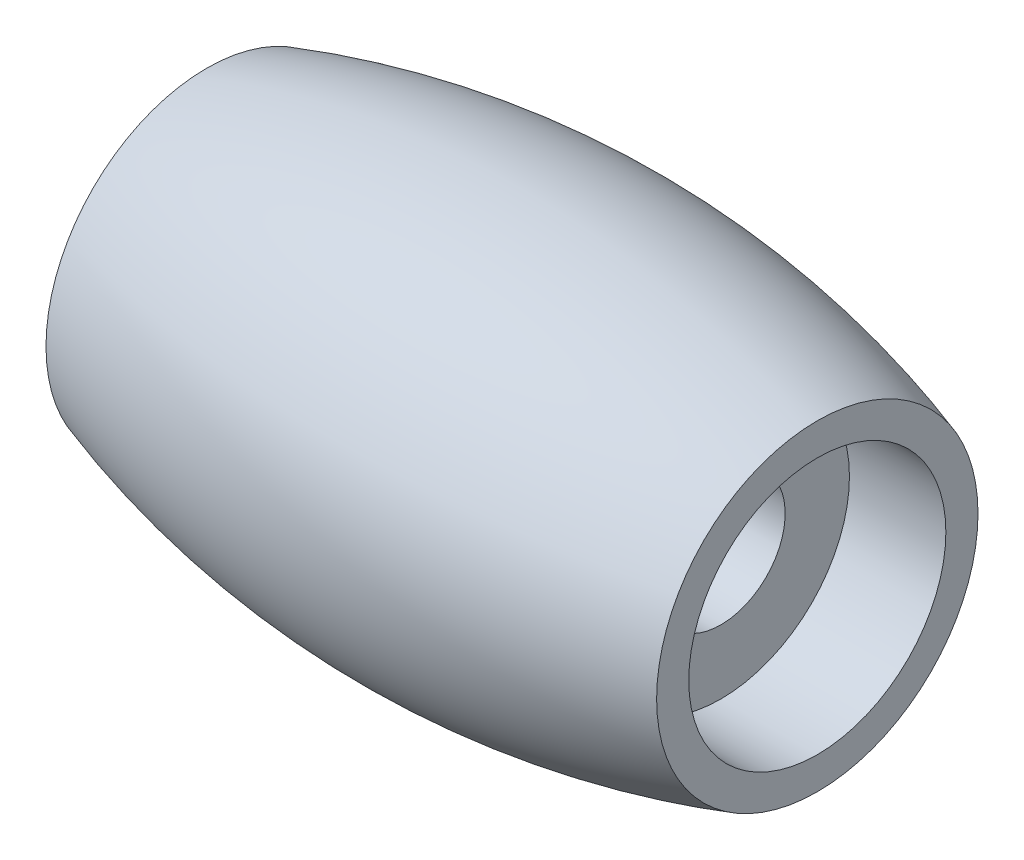
SolidWorks part; units mm, degrees
ref_plane "Front Plane" through (0, 0, 0) normal (0, 0, 1) x (1, 0, 0)
ref_plane "Top Plane" through (0, 0, 0) normal (0, 1, 0) x (1, 0, 0)
ref_plane "Right Plane" through (0, 0, 0) normal (1, 0, 0) x (0, 0, -1)
sketch "Sketch1" plane through (0, 0, 0) normal (0, 0, 1) x (1, 0, 0)
  line L0 (0, 0) -> (20.3808, 0) construction
  line L1 (0, 4) -> (0, 5)
  line L2 (0, 4) -> (3, 4)
  line L3 (3, 4) -> (3, 2)
  line L4 (3, 2) -> (16, 2)
  line L5 (16, 2) -> (16, 4)
  line L6 (16, 4) -> (19, 4)
  line L7 (19, 4) -> (19, 5)
  arc A0 (0, 5) -> (19, 5) centre (9.5, -24.333) cw
  point P13 (9.5, 6.5)
  dimension "D5" = 30.833
  dimension "D1" = 19
  dimension "D2" = 3
  dimension "D3" = 8
  dimension "D4" = 4
  dimension "D6" = 10
  dimension "D7" = 13
revolve "Revolve1" add sketch "Sketch1" angle 360 about L0
sketch "Sketch3" plane through (0, 0, 0) normal (0, 0, 1) x (1, 0, 0)
  line L0 (-0.9954, 0) -> (19.8894, 0) construction
  line L1 (0, 5) -> (0, 5.15)
  line L2 (9.4003, -0.6366) -> (9.4003, 7.1254) construction
  line L4 (0, 5) -> (19, 5)
  line L5 (19, 5) -> (19, 5.15)
  arc A1 (19, 5.15) -> (0, 5.15) centre (9.5, -23.8328) ccw
  dimension "D1" = 30.5
  dimension "D2" = 0.15
revolve "Revolve2" [suppressed] add sketch "Sketch3" angle 360 about L4
pattern_circular "CirPattern2" [suppressed] count 10 over 360
